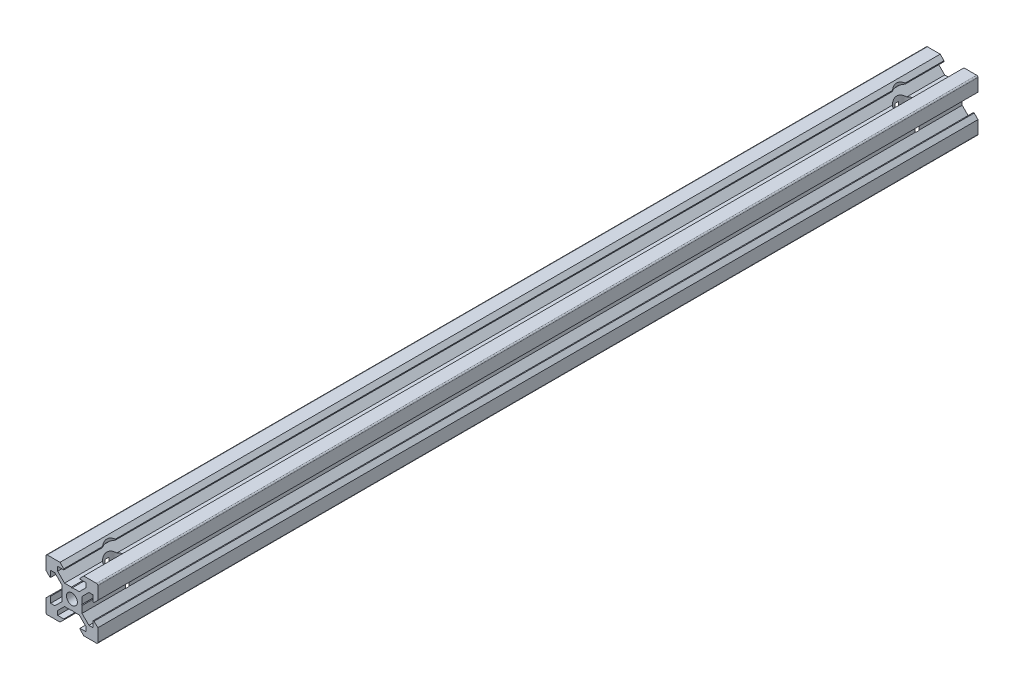
SolidWorks part; units mm, degrees
material "6061-T6 (SS)"
ref_plane "Front Plane" through (0, 0, 0) normal (0, 0, 1) x (1, 0, 0)
ref_plane "Top Plane" through (0, 0, 0) normal (0, 1, 0) x (1, 0, 0)
ref_plane "Right Plane" through (0, 0, 0) normal (1, 0, 0) x (0, 0, -1)
ref_plane "Plane1" through (0, 0, 0) normal (0, 0, -1) x (-1, 0, 0)
sketch "Sketch1" plane through (0, 0, 0) normal (0, 0, -1) x (-1, 0, 0)
  line L0 (-3.9, -0.21) -> (-3.9, -2.8393)
  line L1 (-3.9, -2.8393) -> (-6.5607, -5.5)
  line L2 (-6.5607, -5.5) -> (-8.2, -5.5)
  line L3 (-8.2, -5.5) -> (-8.2, -3.125)
  line L4 (-8.2, -3.125) -> (-8.545, -3.125)
  line L5 (-8.545, -3.125) -> (-10, -4.58)
  line L6 (-10, -4.58) -> (-10, -9.5)
  line L7 (-9.5, -10) -> (-4.58, -10)
  line L8 (-4.58, -10) -> (-3.125, -8.545)
  line L9 (-3.125, -8.545) -> (-3.125, -8.2)
  line L10 (-3.125, -8.2) -> (-5.5, -8.2)
  line L11 (-5.5, -8.2) -> (-5.5, -6.5607)
  line L12 (-5.5, -6.5607) -> (-2.8393, -3.9)
  line L13 (-2.8393, -3.9) -> (-0.21, -3.9)
  line L14 (-0.21, -3.9) -> (0, -3.69)
  line L15 (0, -3.69) -> (0.21, -3.9)
  line L16 (0.21, -3.9) -> (2.8393, -3.9)
  line L17 (2.8393, -3.9) -> (5.5, -6.5607)
  line L18 (5.5, -6.5607) -> (5.5, -8.2)
  line L19 (5.5, -8.2) -> (3.125, -8.2)
  line L20 (3.125, -8.2) -> (3.125, -8.545)
  line L21 (3.125, -8.545) -> (4.58, -10)
  line L22 (4.58, -10) -> (9.5, -10)
  line L23 (10, -9.5) -> (10, -4.58)
  line L24 (10, -4.58) -> (8.545, -3.125)
  line L25 (8.545, -3.125) -> (8.2, -3.125)
  line L26 (8.2, -3.125) -> (8.2, -5.5)
  line L27 (8.2, -5.5) -> (6.5607, -5.5)
  line L28 (6.5607, -5.5) -> (3.9, -2.8393)
  line L29 (3.9, -2.8393) -> (3.9, -0.21)
  line L30 (3.9, -0.21) -> (3.69, 0)
  line L31 (3.69, 0) -> (3.9, 0.21)
  line L32 (3.9, 0.21) -> (3.9, 2.8393)
  line L33 (3.9, 2.8393) -> (6.5607, 5.5)
  line L34 (6.5607, 5.5) -> (8.2, 5.5)
  line L35 (8.2, 5.5) -> (8.2, 3.125)
  line L36 (8.2, 3.125) -> (8.545, 3.125)
  line L37 (8.545, 3.125) -> (10, 4.58)
  line L38 (10, 4.58) -> (10, 9.5)
  line L39 (9.5, 10) -> (4.58, 10)
  line L40 (4.58, 10) -> (3.125, 8.545)
  line L41 (3.125, 8.545) -> (3.125, 8.2)
  line L42 (3.125, 8.2) -> (5.5, 8.2)
  line L43 (5.5, 8.2) -> (5.5, 6.5607)
  line L44 (5.5, 6.5607) -> (2.8393, 3.9)
  line L45 (2.8393, 3.9) -> (0.21, 3.9)
  line L46 (0.21, 3.9) -> (0, 3.69)
  line L47 (0, 3.69) -> (-0.21, 3.9)
  line L48 (-0.21, 3.9) -> (-2.8393, 3.9)
  line L49 (-2.8393, 3.9) -> (-5.5, 6.5607)
  line L50 (-5.5, 6.5607) -> (-5.5, 8.2)
  line L51 (-5.5, 8.2) -> (-3.125, 8.2)
  line L52 (-3.125, 8.2) -> (-3.125, 8.545)
  line L53 (-3.125, 8.545) -> (-4.58, 10)
  line L54 (-4.58, 10) -> (-9.5, 10)
  line L55 (-10, 9.5) -> (-10, 4.58)
  line L56 (-10, 4.58) -> (-8.545, 3.125)
  line L57 (-8.545, 3.125) -> (-8.2, 3.125)
  line L58 (-8.2, 3.125) -> (-8.2, 5.5)
  line L59 (-8.2, 5.5) -> (-6.5607, 5.5)
  line L60 (-6.5607, 5.5) -> (-3.9, 2.8393)
  line L61 (-3.9, 2.8393) -> (-3.9, 0.21)
  line L62 (-3.9, 0.21) -> (-3.69, 0)
  line L63 (-3.69, 0) -> (-3.9, -0.21)
  circle A0 centre (0, 0) radius 2.1
  arc A1 (-10, -9.5) -> (-9.5, -10) centre (-9.5, -9.5) ccw
  arc A2 (9.5, -10) -> (10, -9.5) centre (9.5, -9.5) ccw
  arc A3 (10, 9.5) -> (9.5, 10) centre (9.5, 9.5) ccw
  arc A4 (-9.5, 10) -> (-10, 9.5) centre (-9.5, 9.5) ccw
extrude "Boss-Extrude1" add sketch "Sketch1" against normal blind 500
ref_plane "cut plane" through (0, 0, 160.35) normal (0, 0, 1) x (1, 0, 0)
split "Split1" trim tools "cut plane" bodies to split 103 resulting bodies 105
sketch "Sketch2" plane through (0, 10, 0) normal (0, 1, 0) x (1, 0, 0)
  line L0 (0, -500) -> (0, -160.35) construction
  line L1 (0, -500) -> (0, -160.35) construction
  line L2 (0, -330.175) -> (-38.7772, -330.175) construction
  circle A0 centre (0, -177.775) radius 3.9687
  circle A1 centre (0, -482.575) radius 3.9688
  dimension "D1" = 7.9375
  dimension "D2" = 304.8
  dimension "D3" = 152.4
extrude "Cut-Extrude1" cut sketch "Sketch2" against normal up to surface (20 mm away) up to face at (7.04, -10, 330.175)
hole_wizard "M5x0.8 Tapped Hole1" positions "Sketch4" profile "Sketch5" tap size "M5x0.8" standard "ANSI Metric"
sketch "Sketch4" plane through (0, 0, 500) normal (0, 0, 1) x (1, 0, 0)
  point P0 (0, 0)
sketch "Sketch5" plane through (0, 0, 500) normal (1, 0, 0) x (0, -1, 0)
  line L0 (0, 0) -> (0, 15.2318)
  line L1 (0, 15.2318) -> (2.1, 13.97)
  line L2 (2.1, 13.97) -> (2.1, 0)
  line L5 (2.1, 0) -> (0, 0)
  line L10 (0, 15.2318) -> (-2.1, 13.97) construction
  line L11 (0, -6.35) -> (0, 107.95) construction
  dimension "Tap Drill Dia." = 4.2
  dimension "Tap Drill Depth" = 13.97
  dimension "Drill Angle" = 118
hole_wizard "M5x0.8 Tapped Hole2" positions "Sketch7" profile "Sketch6" tap size "M5x0.8" standard "ANSI Metric"
sketch "Sketch7" plane through (0, 0, 160.35) normal (0, 0, -1) x (-1, 0, 0)
  point P0 (0, 0)
sketch "Sketch6" plane through (0, 0, 160.35) normal (1, 0, 0) x (0, 1, 0)
  line L0 (0, 0) -> (0, 15.2318)
  line L1 (0, 15.2318) -> (2.1, 13.97)
  line L2 (2.1, 13.97) -> (2.1, 0)
  line L5 (2.1, 0) -> (0, 0)
  line L10 (0, 15.2318) -> (-2.1, 13.97) construction
  line L11 (0, -6.35) -> (0, 107.95) construction
  dimension "Tap Drill Dia." = 4.2
  dimension "Tap Drill Depth" = 13.97
  dimension "Drill Angle" = 118
